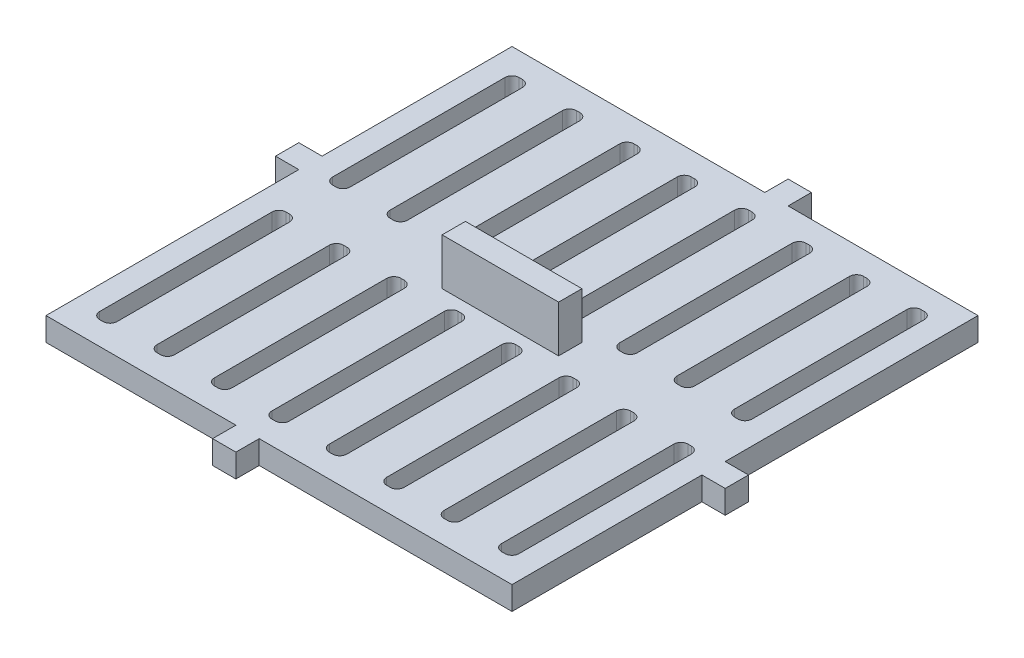
SolidWorks part; units mm, degrees
ref_plane "Front Plane" through (0, 0, 0) normal (0, 0, 1) x (1, 0, 0)
ref_plane "Top Plane" through (0, 0, 0) normal (0, 1, 0) x (1, 0, 0)
ref_plane "Right Plane" through (0, 0, 0) normal (1, 0, 0) x (0, 0, -1)
sketch "Sketch2" plane through (0, 0, 0) normal (0, 1, 0) x (1, 0, 0)
  line L1 (0, 0) -> (50.8, 0)
  line L2 (0, 0) -> (0, -50.8)
  line L3 (0, -50.8) -> (50.8, -50.8)
  line L4 (50.8, 0) -> (50.8, -50.8)
  dimension "D1" = 50.8
  dimension "D2" = 50.8
extrude "Boss-Extrude1" add sketch "Sketch2" along normal blind 2.54
sketch "Sketch3" plane through (0, 2.54, 0) normal (0, 1, 0) x (1, 0, 0)
  line L0 (8.7993, -3.302) -> (8.7993, -22.098)
  line L1 (3.302, -2.54) -> (3.683, -2.54)
  line L2 (2.54, -3.302) -> (2.54, -22.098)
  line L3 (3.302, -22.86) -> (3.683, -22.86)
  line L4 (4.445, -3.302) -> (4.445, -22.098)
  line L5 (9.5613, -2.54) -> (9.9423, -2.54)
  line L6 (10.7043, -3.302) -> (10.7043, -22.098)
  line L7 (9.5613, -22.86) -> (9.9423, -22.86)
  line L8 (15.0586, -3.302) -> (15.0586, -22.098)
  line L9 (15.8206, -2.54) -> (16.2016, -2.54)
  line L10 (16.9636, -3.302) -> (16.9636, -22.098)
  line L11 (15.8206, -22.86) -> (16.2016, -22.86)
  line L12 (21.3179, -3.302) -> (21.3179, -22.098)
  line L13 (22.0799, -2.54) -> (22.4609, -2.54)
  line L14 (23.2229, -3.302) -> (23.2229, -22.098)
  line L15 (22.0799, -22.86) -> (22.4609, -22.86)
  line L16 (27.5771, -3.302) -> (27.5771, -22.098)
  line L17 (28.3391, -2.54) -> (28.7201, -2.54)
  line L18 (29.4821, -3.302) -> (29.4821, -22.098)
  line L19 (28.3391, -22.86) -> (28.7201, -22.86)
  line L20 (33.8364, -3.302) -> (33.8364, -22.098)
  line L21 (34.5984, -2.54) -> (34.9794, -2.54)
  line L22 (35.7414, -3.302) -> (35.7414, -22.098)
  line L23 (34.5984, -22.86) -> (34.9794, -22.86)
  line L24 (40.0957, -3.302) -> (40.0957, -22.098)
  line L25 (40.8577, -2.54) -> (41.2387, -2.54)
  line L26 (42.0007, -3.302) -> (42.0007, -22.098)
  line L27 (40.8577, -22.86) -> (41.2387, -22.86)
  line L28 (46.355, -3.302) -> (46.355, -22.098)
  line L29 (47.117, -2.54) -> (47.498, -2.54)
  line L30 (48.26, -3.302) -> (48.26, -22.098)
  line L31 (47.117, -22.86) -> (47.498, -22.86)
  line L32 (0, 0) -> (0, -50.8) construction
  line L34 (2.54, -28.702) -> (2.54, -47.498)
  line L35 (3.302, -27.94) -> (3.683, -27.94)
  line L36 (4.445, -28.702) -> (4.445, -47.498)
  line L37 (3.302, -48.26) -> (3.683, -48.26)
  line L38 (8.7993, -28.702) -> (8.7993, -47.498)
  line L39 (9.5613, -48.26) -> (9.9423, -48.26)
  line L40 (10.7043, -28.702) -> (10.7043, -47.498)
  line L41 (9.5613, -27.94) -> (9.9423, -27.94)
  line L42 (15.0586, -28.702) -> (15.0586, -47.498)
  line L43 (15.8206, -48.26) -> (16.2016, -48.26)
  line L44 (16.9636, -28.702) -> (16.9636, -47.498)
  line L45 (15.8206, -27.94) -> (16.2016, -27.94)
  line L46 (21.3179, -28.702) -> (21.3179, -47.498)
  line L47 (22.0799, -48.26) -> (22.4609, -48.26)
  line L48 (23.2229, -28.702) -> (23.2229, -47.498)
  line L49 (22.0799, -27.94) -> (22.4609, -27.94)
  line L50 (27.5771, -28.702) -> (27.5771, -47.498)
  line L51 (28.3391, -48.26) -> (28.7201, -48.26)
  line L52 (29.4821, -28.702) -> (29.4821, -47.498)
  line L53 (28.3391, -27.94) -> (28.7201, -27.94)
  line L54 (33.8364, -28.702) -> (33.8364, -47.498)
  line L55 (34.5984, -48.26) -> (34.9794, -48.26)
  line L56 (35.7414, -28.702) -> (35.7414, -47.498)
  line L57 (34.5984, -27.94) -> (34.9794, -27.94)
  line L58 (40.0957, -28.702) -> (40.0957, -47.498)
  line L59 (40.8577, -48.26) -> (41.2387, -48.26)
  line L60 (42.0007, -28.702) -> (42.0007, -47.498)
  line L61 (40.8577, -27.94) -> (41.2387, -27.94)
  line L62 (46.355, -28.702) -> (46.355, -47.498)
  line L63 (47.117, -48.26) -> (47.498, -48.26)
  line L64 (48.26, -28.702) -> (48.26, -47.498)
  line L65 (47.117, -27.94) -> (47.498, -27.94)
  line L66 (0, -50.8) -> (50.8, -50.8) construction
  line L67 (50.8, 0) -> (0, 0) construction
  line L68 (50.8, -50.8) -> (50.8, 0) construction
  arc A0 (15.0586, -28.702) -> (15.8206, -27.94) centre (15.8206, -28.702) cw
  arc A1 (16.9636, -28.702) -> (16.2016, -27.94) centre (16.2016, -28.702) ccw
  arc A2 (21.3179, -28.702) -> (22.0799, -27.94) centre (22.0799, -28.702) cw
  arc A3 (23.2229, -28.702) -> (22.4609, -27.94) centre (22.4609, -28.702) ccw
  arc A4 (27.5771, -28.702) -> (28.3391, -27.94) centre (28.3391, -28.702) cw
  arc A5 (29.4821, -28.702) -> (28.7201, -27.94) centre (28.7201, -28.702) ccw
  arc A6 (33.8364, -28.702) -> (34.5984, -27.94) centre (34.5984, -28.702) cw
  arc A7 (35.7414, -28.702) -> (34.9794, -27.94) centre (34.9794, -28.702) ccw
  arc A8 (40.0957, -28.702) -> (40.8577, -27.94) centre (40.8577, -28.702) cw
  arc A9 (42.0007, -28.702) -> (41.2387, -27.94) centre (41.2387, -28.702) ccw
  arc A10 (46.355, -28.702) -> (47.117, -27.94) centre (47.117, -28.702) cw
  arc A11 (48.26, -28.702) -> (47.498, -27.94) centre (47.498, -28.702) ccw
  arc A12 (47.498, -48.26) -> (48.26, -47.498) centre (47.498, -47.498) ccw
  arc A13 (46.355, -47.498) -> (47.117, -48.26) centre (47.117, -47.498) ccw
  arc A14 (41.2387, -48.26) -> (42.0007, -47.498) centre (41.2387, -47.498) ccw
  arc A15 (40.0957, -47.498) -> (40.8577, -48.26) centre (40.8577, -47.498) ccw
  arc A16 (34.9794, -48.26) -> (35.7414, -47.498) centre (34.9794, -47.498) ccw
  arc A17 (33.8364, -47.498) -> (34.5984, -48.26) centre (34.5984, -47.498) ccw
  arc A18 (28.7201, -48.26) -> (29.4821, -47.498) centre (28.7201, -47.498) ccw
  arc A19 (27.5771, -47.498) -> (28.3391, -48.26) centre (28.3391, -47.498) ccw
  arc A20 (22.4609, -48.26) -> (23.2229, -47.498) centre (22.4609, -47.498) ccw
  arc A21 (21.3179, -47.498) -> (22.0799, -48.26) centre (22.0799, -47.498) ccw
  arc A22 (16.2016, -48.26) -> (16.9636, -47.498) centre (16.2016, -47.498) ccw
  arc A23 (15.0586, -47.498) -> (15.8206, -48.26) centre (15.8206, -47.498) ccw
  arc A24 (9.9423, -48.26) -> (10.7043, -47.498) centre (9.9423, -47.498) ccw
  arc A25 (8.7993, -47.498) -> (9.5613, -48.26) centre (9.5613, -47.498) ccw
  arc A26 (4.445, -47.498) -> (3.683, -48.26) centre (3.683, -47.498) cw
  arc A27 (2.54, -47.498) -> (3.302, -48.26) centre (3.302, -47.498) ccw
  arc A28 (2.54, -28.702) -> (3.302, -27.94) centre (3.302, -28.702) cw
  arc A29 (3.683, -27.94) -> (4.445, -28.702) centre (3.683, -28.702) cw
  arc A30 (10.7043, -28.702) -> (9.9423, -27.94) centre (9.9423, -28.702) ccw
  arc A31 (8.7993, -28.702) -> (9.5613, -27.94) centre (9.5613, -28.702) cw
  arc A32 (15.0586, -22.098) -> (15.8206, -22.86) centre (15.8206, -22.098) ccw
  arc A33 (16.9636, -22.098) -> (16.2016, -22.86) centre (16.2016, -22.098) cw
  arc A34 (21.3179, -22.098) -> (22.0799, -22.86) centre (22.0799, -22.098) ccw
  arc A35 (23.2229, -22.098) -> (22.4609, -22.86) centre (22.4609, -22.098) cw
  arc A36 (27.5771, -22.098) -> (28.3391, -22.86) centre (28.3391, -22.098) ccw
  arc A37 (29.4821, -22.098) -> (28.7201, -22.86) centre (28.7201, -22.098) cw
  arc A38 (33.8364, -22.098) -> (34.5984, -22.86) centre (34.5984, -22.098) ccw
  arc A39 (35.7414, -22.098) -> (34.9794, -22.86) centre (34.9794, -22.098) cw
  arc A40 (40.0957, -22.098) -> (40.8577, -22.86) centre (40.8577, -22.098) ccw
  arc A41 (42.0007, -22.098) -> (41.2387, -22.86) centre (41.2387, -22.098) cw
  arc A42 (46.355, -22.098) -> (47.117, -22.86) centre (47.117, -22.098) ccw
  arc A43 (48.26, -22.098) -> (47.498, -22.86) centre (47.498, -22.098) cw
  arc A44 (47.498, -2.54) -> (48.26, -3.302) centre (47.498, -3.302) cw
  arc A45 (46.355, -3.302) -> (47.117, -2.54) centre (47.117, -3.302) cw
  arc A46 (41.2387, -2.54) -> (42.0007, -3.302) centre (41.2387, -3.302) cw
  arc A47 (40.0957, -3.302) -> (40.8577, -2.54) centre (40.8577, -3.302) cw
  arc A48 (34.9794, -2.54) -> (35.7414, -3.302) centre (34.9794, -3.302) cw
  arc A49 (33.8364, -3.302) -> (34.5984, -2.54) centre (34.5984, -3.302) cw
  arc A50 (28.7201, -2.54) -> (29.4821, -3.302) centre (28.7201, -3.302) cw
  arc A51 (27.5771, -3.302) -> (28.3391, -2.54) centre (28.3391, -3.302) cw
  arc A52 (22.4609, -2.54) -> (23.2229, -3.302) centre (22.4609, -3.302) cw
  arc A53 (21.3179, -3.302) -> (22.0799, -2.54) centre (22.0799, -3.302) cw
  arc A54 (16.2016, -2.54) -> (16.9636, -3.302) centre (16.2016, -3.302) cw
  arc A55 (15.0586, -3.302) -> (15.8206, -2.54) centre (15.8206, -3.302) cw
  arc A56 (8.7993, -3.302) -> (9.5613, -2.54) centre (9.5613, -3.302) cw
  arc A57 (9.9423, -2.54) -> (10.7043, -3.302) centre (9.9423, -3.302) cw
  arc A58 (10.7043, -22.098) -> (9.9423, -22.86) centre (9.9423, -22.098) cw
  arc A59 (8.7993, -22.098) -> (9.5613, -22.86) centre (9.5613, -22.098) ccw
  arc A60 (3.683, -22.86) -> (4.445, -22.098) centre (3.683, -22.098) ccw
  arc A61 (2.54, -22.098) -> (3.302, -22.86) centre (3.302, -22.098) ccw
  arc A62 (3.683, -2.54) -> (4.445, -3.302) centre (3.683, -3.302) cw
  arc A63 (3.302, -2.54) -> (2.54, -3.302) centre (3.302, -3.302) ccw
  point P192 (4.445, -22.86)
  point P197 (4.445, -2.54)
  point P200 (2.54, -2.54)
  dimension "D8" = 0.762
  dimension "D1" = 1.905
  dimension "D2" = 20.32
  dimension "D4" = 2.54
  dimension "D5" = 2
  dimension "D6" = 2.54
  dimension "D7" = 2.54
  dimension "D9" = 2.54
  dimension "D3" = 8
extrude "Cut-Extrude1" cut sketch "Sketch3" against normal up to surface (2.54 mm away) contours L2 A61 L3 A60 L4 A62 L1 A63 | A55 L9 A54 L10 A33 L11 A32 L8 | A31 L41 A30 L40 A24 L39 A25 L38 | A29 L35 A28 L34 A27 L37 A26 L36 | A23 L43 A22 L44 A1 L45 A0 L42 | A21 L47 A20 L48 A3 L49 A2 L46 | A53 L13 A52 L14 A35 L15 A34 L12 | L0 A59 L7 A58 L6 A57 L5 A56 | A51 L17 A50 L18 A37 L19 A36 L16 | A49 L21 A48 L22 A39 L23 A38 L20 | A47 L25 A46 L26 A41 L27 A40 L24 | A45 L29 A44 L30 A43 L31 A42 L28 | A13 L63 A12 L64 A11 L65 A10 L62 | A15 L59 A14 L60 A9 L61 A8 L58 | A17 L55 A16 L56 A7 L57 A6 L54 | A19 L51 A18 L52 A5 L53 A4 L50 up to face at (25.4, 0, 25.4)
sketch "Sketch6" plane through (0, 0, 50.8) normal (0, 0, 1) x (1, 0, 0)
  line L0 (20.701, 2.54) -> (20.701, 0)
  line L1 (0, 2.54) -> (50.8, 2.54) construction
  line L2 (0, 0) -> (50.8, 0) construction
  line L3 (20.701, 0) -> (23.241, 0)
  line L4 (23.241, 0) -> (23.241, 2.54)
  line L5 (23.241, 2.54) -> (20.701, 2.54)
  line L6 (0, 2.54) -> (0, 0) construction
  dimension "D1" = 20.701
  dimension "D2" = 2.54
extrude "Boss-Extrude2" add sketch "Sketch6" along normal blind 2.54
sketch "Sketch7" plane through (0, 0, 0) normal (-1, 0, 0) x (0, 0, 1)
  line L0 (20.701, 2.54) -> (20.701, 0)
  line L1 (0, 2.54) -> (50.8, 2.54) construction
  line L2 (0, 0) -> (50.8, 0) construction
  line L3 (20.701, 0) -> (23.241, 0)
  line L4 (23.241, 0) -> (23.241, 2.54)
  line L5 (23.241, 2.54) -> (20.701, 2.54)
  line L6 (0, 2.54) -> (0, 0) construction
  dimension "D1" = 2.54
  dimension "D2" = 20.701
extrude "Boss-Extrude3" add sketch "Sketch7" along normal blind 2.54
sketch "Sketch8" plane through (0, 0, 0) normal (0, 0, -1) x (-1, 0, 0)
  line L0 (-50.8, 2.54) -> (0, 2.54) construction
  line L1 (-30.099, 2.54) -> (-27.559, 2.54)
  line L2 (-30.099, 2.54) -> (-30.099, 0)
  line L3 (-30.099, 0) -> (-27.559, 0)
  line L4 (-27.559, 2.54) -> (-27.559, 0)
  line L5 (-50.8, 0) -> (0, 0) construction
  line L6 (-50.8, 2.54) -> (-50.8, 0) construction
  dimension "D1" = 2.54
  dimension "D2" = 20.701
extrude "Boss-Extrude4" add sketch "Sketch8" along normal blind 2.54
sketch "Sketch9" plane through (50.8, 0, 0) normal (1, 0, 0) x (0, 0, -1)
  line L0 (-50.8, 2.54) -> (0, 2.54) construction
  line L1 (-30.099, 2.54) -> (-27.559, 2.54)
  line L2 (-30.099, 2.54) -> (-30.099, 0)
  line L3 (-30.099, 0) -> (-27.559, 0)
  line L4 (-27.559, 2.54) -> (-27.559, 0)
  line L5 (-50.8, 0) -> (0, 0) construction
  line L6 (-50.8, 2.54) -> (-50.8, 0) construction
  dimension "D1" = 2.54
  dimension "D2" = 20.701
extrude "Boss-Extrude5" add sketch "Sketch9" along normal blind 2.54
sketch "Sketch10" plane through (0, 2.54, 0) normal (0, 1, 0) x (1, 0, 0)
  line L0 (0, 0) -> (50.8, 0) construction
  line L1 (19.05, -24.13) -> (31.75, -24.13)
  line L2 (19.05, -24.13) -> (19.05, -26.67)
  line L3 (19.05, -26.67) -> (31.75, -26.67)
  line L4 (31.75, -24.13) -> (31.75, -26.67)
  line L7 (0, -50.8) -> (20.701, -50.8) construction
  point P8 (25.4, 0)
  point P9 (25.4, -24.13)
  point P14 (19.05, -25.4)
  dimension "D1" = 2.54
  dimension "D2" = 12.7
  dimension "D3" = 25.4
extrude "Boss-Extrude6" add sketch "Sketch10" along normal blind 5.08
